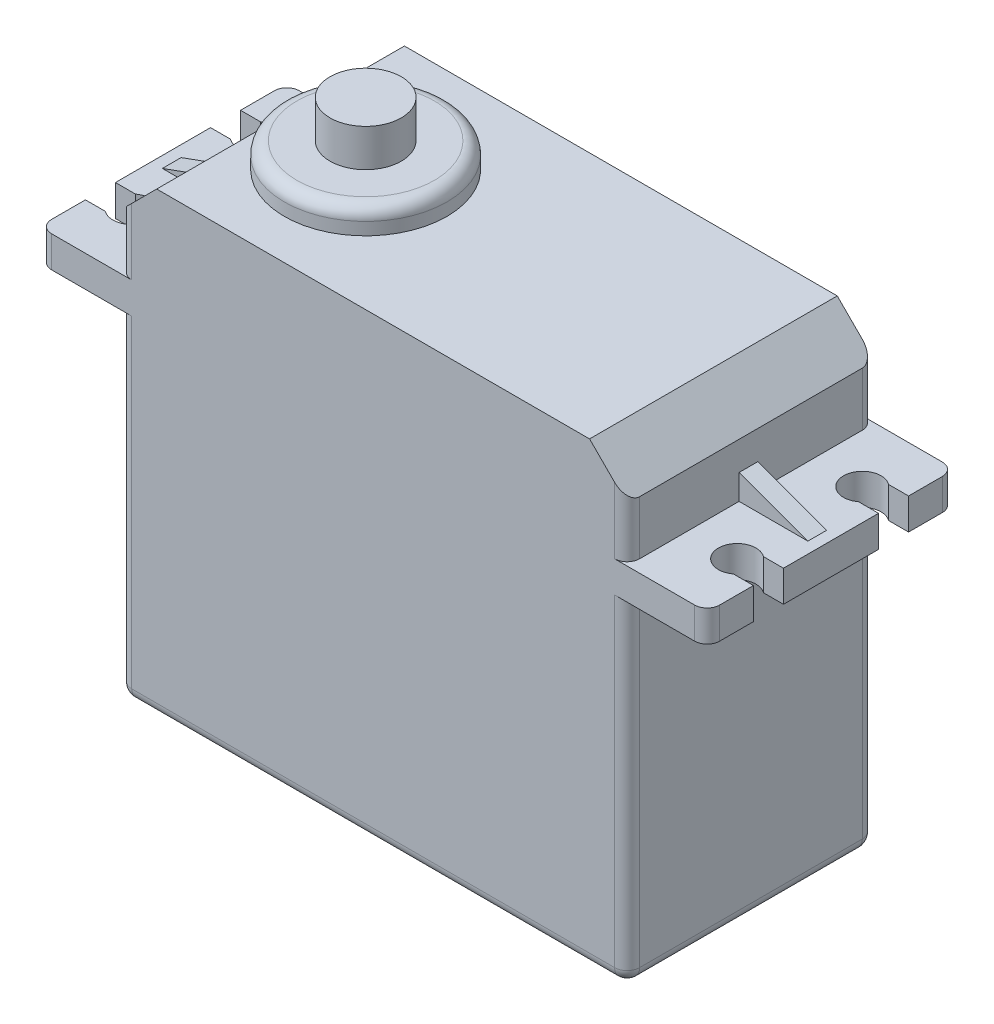
SolidWorks part; units mm, degrees
ref_plane "Front Plane" through (0, 0, 0) normal (0, 0, 1) x (1, 0, 0)
ref_plane "Top Plane" through (0, 0, 0) normal (0, 1, 0) x (1, 0, 0)
ref_plane "Right Plane" through (0, 0, 0) normal (1, 0, 0) x (0, 0, -1)
sketch "Sketch1" plane through (0, 0, 0) normal (0, 0, 1) x (1, 0, 0)
  line L0 (0, 0) -> (40.6, 0)
  line L1 (0, 0) -> (0, 26.8)
  line L2 (0, 26.8) -> (-6.4, 26.8)
  line L3 (-6.4, 26.8) -> (-6.4, 29.3)
  line L4 (-6.4, 29.3) -> (0, 29.3)
  line L5 (0, 29.3) -> (0, 33.6)
  line L6 (3, 36.6) -> (37.6, 36.6)
  line L7 (40.6, 33.6) -> (40.6, 29.3)
  line L8 (40.6, 29.3) -> (47, 29.3)
  line L9 (47, 29.3) -> (47, 26.8)
  line L10 (47, 26.8) -> (40.6, 26.8)
  line L11 (40.6, 26.8) -> (40.6, 0)
  line L12 (0, 33.6) -> (3, 36.6)
  line L13 (37.6, 36.6) -> (40.6, 33.6)
  point P7 (0, 36.6)
  point P8 (40.6, 36.6)
  dimension "D1" = 40.6
  dimension "D2" = 26.8
  dimension "D3" = 2.5
  dimension "D4" = 36.6
  dimension "D5" = 53.4
extrude "Main Servo Body" add sketch "Sketch1" along normal blind 19.8
sketch "Sketch2" plane through (0, 29.3, 0) normal (0, 1, 0) x (1, 0, 0)
  line L0 (-6.4, -19.8) -> (-6.4, 0) construction
  line L1 (47, -19.8) -> (47, 0) construction
  line L2 (-6.4, -3.7) -> (-4.8, -3.7)
  line L3 (-6.4, -6.1) -> (-4.8, -6.1)
  line L4 (-6.4, -3.7) -> (-6.4, -6.1)
  line L5 (45.4, -3.7) -> (47, -3.7)
  line L6 (47, -3.7) -> (47, -6.1)
  line L7 (45.4, -13.7) -> (47, -13.7)
  line L8 (45.4, -6.1) -> (47, -6.1)
  line L9 (47, -16.1) -> (47, -13.7)
  line L10 (45.4, -16.1) -> (47, -16.1)
  line L11 (-6.4, -16.1) -> (-6.4, -13.7)
  line L12 (-6.4, -13.7) -> (-4.8, -13.7)
  line L13 (-6.4, -16.1) -> (-4.8, -16.1)
  line L14 (-6.4, -9.9) -> (47, -9.9) construction
  line L15 (0, -19.8) -> (0, 0) construction
  arc A0 (45.4, -3.7) -> (45.4, -6.1) centre (44.5, -4.9) ccw
  arc A1 (-4.8, -6.1) -> (-4.8, -3.7) centre (-3.9, -4.9) ccw
  arc A2 (-4.8, -13.7) -> (-4.8, -16.1) centre (-3.9, -14.9) cw
  arc A3 (45.4, -16.1) -> (45.4, -13.7) centre (44.5, -14.9) cw
  dimension "D1" = 3
  dimension "D2" = 5
  dimension "D3" = 2.5
  dimension "D4" = 2.5
  dimension "D5" = 2.4
  dimension "D6" = 2.4
extrude "Servo Bracket" cut sketch "Sketch2" against normal through all
sketch "Sketch3" plane through (0, 36.6, 0) normal (0, 1, 0) x (1, 0, 0)
  circle A0 centre (10, -10.1) radius 6.5
  dimension "D1" = 13
  dimension "D2" = 10
  dimension "D3" = 10.1
extrude "Servo Axis 1" add sketch "Sketch3" along normal blind 2
ref_plane "Plane for Servo Brackets Support" through (0, 0, 10.1) normal (0, 0, 1) x (1, 0, 0)
sketch "Sketch4" plane through (0, 0, 10.1) normal (0, 0, 1) x (1, 0, 0)
  line L0 (-5.5, 29.3) -> (0, 31.3)
  line L1 (0, 29.3) -> (-6.4, 29.3) construction
  line L2 (0, 33.6) -> (0, 29.3) construction
  line L3 (0, 31.3) -> (0, 29.3)
  line L4 (0, 29.3) -> (-5.5, 29.3)
  line L5 (40.6, 29.3) -> (46.1, 29.3)
  line L7 (46.1, 29.3) -> (40.6, 31.3)
  line L9 (40.6, 31.3) -> (40.6, 29.3)
  line L10 (47, 29.3) -> (40.6, 29.3) construction
  dimension "D1" = 5.5
  dimension "D2" = 2
extrude "Servo Bracket Support" add sketch "Sketch4" along normal mid plane 1.5
sketch "Sketch5" plane through (0, 38.6, 0) normal (0, 1, 0) x (1, 0, 0)
  circle A0 centre (10, -10.1) radius 2.85
  circle A1 centre (10, -10.1) radius 6.5 construction
  dimension "D1" = 5.7
extrude "Servo Axis 2" add sketch "Sketch5" along normal blind 3
sketch "Sketch6" plane through (0, 0, 0) normal (-1, 0, 0) x (0, 0, 1)
  circle A0 centre (10.1, 6) radius 2.5
  dimension "D1" = 5
  dimension "D2" = 10.1
  dimension "D3" = 6
extrude "Servo Wires" add sketch "Sketch6" along normal blind 2
fillet "Servo Contouring" radius 1 17 edges at (-6.4, 28.05, 19.8) (10, 38.6, 16.6) (-6.4, 28.05, 0) (0, 13.4, 0) (47, 28.05, 0) (47, 28.05, 19.8) (40.6, 13.4, 0) (40.6, 13.4, 19.8) (40.6, 0, 9.9) (20.3, 0, 0) (0, 0, 9.9) (20.3, 0, 19.8) (0, 13.4, 19.8) (40.6, 31.45, 0) (40.6, 31.45, 19.8) (0, 31.45, 0) (0, 31.45, 19.8)
